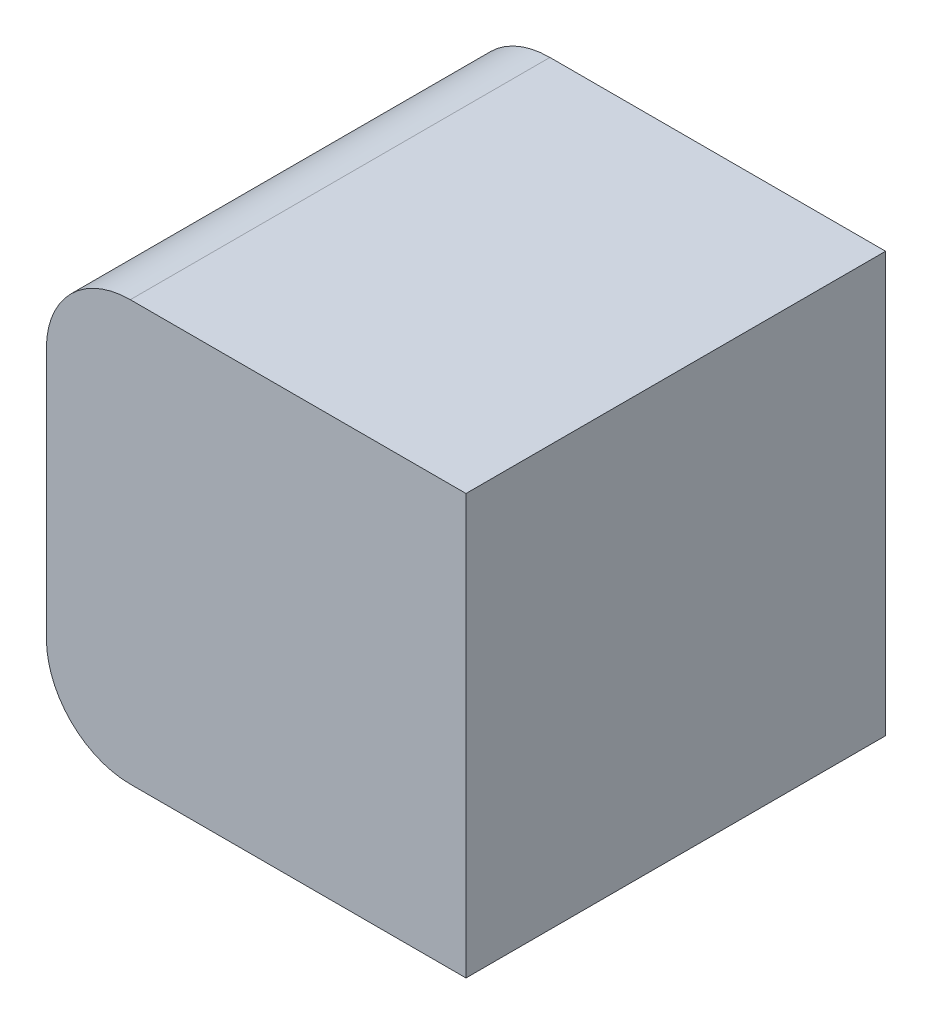
SolidWorks part; units mm, degrees
material "Wrought Stainless Steel"
ref_plane "Front Plane" through (0, 0, 0) normal (0, 0, 1) x (1, 0, 0)
ref_plane "Top Plane" through (0, 0, 0) normal (0, 1, 0) x (1, 0, 0)
ref_plane "Right Plane" through (0, 0, 0) normal (1, 0, 0) x (0, 0, -1)
sketch "Sketch5" plane through (0, 0, 0) normal (1, 0, 0) x (0, 0, -1)
  line L0 (0, 0) -> (0, 1000)
  line L1 (0, 1000) -> (1000, 1000)
  line L2 (1000, 1000) -> (1000, 0)
  line L3 (1000, 0) -> (0, 0)
  dimension "D1" = 1000
  dimension "D2" = 1000
  dimension "D3" = 1000
extrude "Boss-Extrude2" add sketch "Sketch5" along normal blind 1000
ref_plane "Plane2" through (500, 0, 0) normal (1, 0, 0) x (0, 0, -1)
sketch "Sketch6" plane through (500, 0, 0) normal (1, 0, 0) x (0, 0, -1)
  line L0 (83.2, 500) -> (916.8, 500)
  arc A0 (83.2, 500) -> (916.8, 500) centre (500, 500) cw
revolve "Cut-Revolve5" cut sketch "Sketch6" angle 360 about L0
sketch "Sketch7" plane through (0, 0, 0) normal (1, 0, 0) x (0, 0, -1)
  line L0 (0, 500) -> (1000, 500)
  line L1 (0, 1000) -> (0, 0) construction
  line L2 (1000, 0) -> (1000, 1000) construction
  circle A0 centre (500, 500) radius 250
extrude "Cut-Extrude2" cut sketch "Sketch7" along normal blind 400 contours A0
fillet "Fillet1" radius 200 2 edges at (0, 1000, -500) (0, 0, -500)
